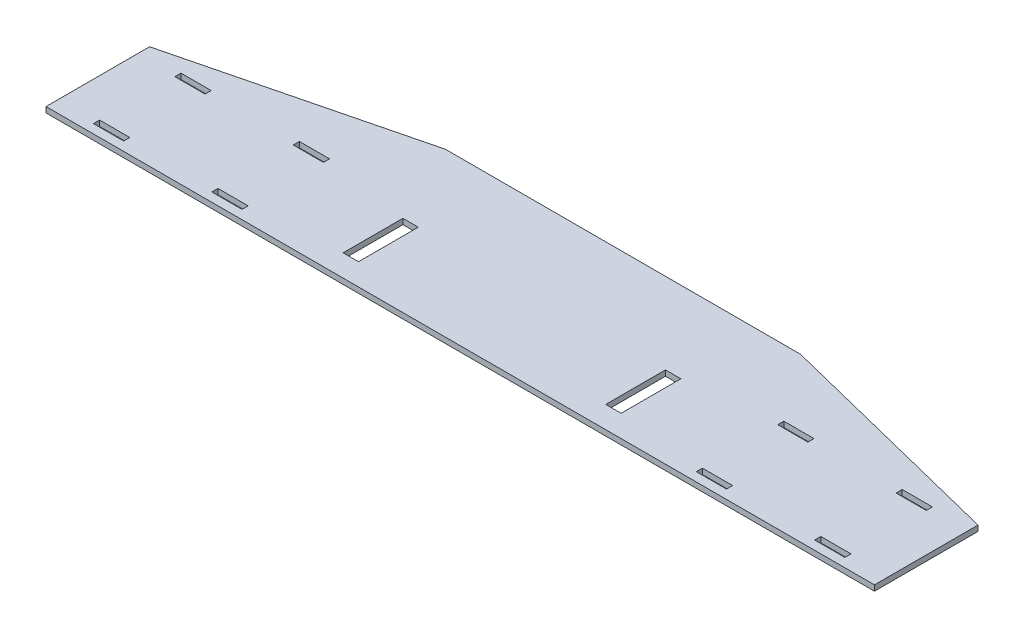
SolidWorks part; units mm, degrees
material "Plain Carbon Steel"
ref_plane "Front Plane" through (0, 0, 0) normal (0, 0, 1) x (1, 0, 0)
ref_plane "Top Plane" through (0, 0, 0) normal (0, 1, 0) x (1, 0, 0)
ref_plane "Right Plane" through (0, 0, 0) normal (1, 0, 0) x (0, 0, -1)
sketch "Sketch1" plane through (0, 0, 0) normal (0, 1, 0) x (1, 0, 0)
  line L1 (-355.6, 0) -> (355.6, 0)
  line L2 (-355.6, 0) -> (-355.6, 139.7)
  line L3 (-355.6, 139.7) -> (355.6, 139.7)
  line L4 (355.6, 0) -> (355.6, 139.7)
  dimension "D1" = 711.2
  dimension "D2" = 139.7
extrude "Boss-Extrude1" add sketch "Sketch1" along normal blind 4.7625
sketch "Sketch2" plane through (0, 4.7625, 0) normal (0, 1, 0) x (1, 0, 0)
  line L0 (-355.6, 88.9) -> (-152.4, 139.7)
  line L1 (-355.6, 139.7) -> (-355.6, 0) construction
  line L2 (355.6, 139.7) -> (-355.6, 139.7) construction
  line L3 (-152.4, 139.7) -> (-355.6, 139.7)
  line L4 (-355.6, 139.7) -> (-355.6, 88.9)
  line L5 (355.6, 139.7) -> (152.4, 139.7)
  line L6 (152.4, 139.7) -> (355.6, 88.9)
  line L7 (355.6, 0) -> (355.6, 139.7) construction
  line L8 (355.6, 88.9) -> (355.6, 139.7)
  dimension "D1" = 203.2
  dimension "D2" = 50.8
extrude "Cut-Extrude1" cut sketch "Sketch2" against normal through all
sketch "Sketch3" plane through (0, 0, 0) normal (0, -1, 0) x (-1, 0, 0)
  line L0 (-119.3165, 70.104) -> (-106.1085, 70.104)
  line L1 (119.0625, 19.05) -> (106.3625, 19.05)
  line L2 (119.0625, 19.05) -> (119.0625, 69.85)
  line L3 (119.0625, 69.85) -> (106.3625, 69.85)
  line L4 (106.3625, 19.05) -> (106.3625, 69.85)
  line L5 (-119.0625, 19.05) -> (-106.3625, 19.05)
  line L6 (-119.0625, 19.05) -> (-119.0625, 69.85)
  line L7 (-119.0625, 69.85) -> (-106.3625, 69.85)
  line L8 (-106.3625, 19.05) -> (-106.3625, 69.85)
  line L9 (-106.1085, 18.796) -> (-106.1085, 70.104)
  line L10 (-119.3165, 18.796) -> (-106.1085, 18.796)
  line L11 (-119.3165, 18.796) -> (-119.3165, 70.104)
  line L12 (119.3165, 18.796) -> (106.1085, 18.796)
  line L13 (106.1085, 18.796) -> (106.1085, 70.104)
  line L14 (119.3165, 70.104) -> (106.1085, 70.104)
  line L15 (119.3165, 18.796) -> (119.3165, 70.104)
  dimension "D1" = 0.254
extrude "Cut-Extrude2" cut sketch "Sketch3" against normal through all
sketch "Sketch4" plane through (0, 0, 0) normal (0, -1, 0) x (1, 0, 0)
  line L0 (119.0625, -82.55) -> (322.2625, -82.55) construction
  line L1 (322.2625, -82.55) -> (296.8625, -82.55)
  line L2 (322.2625, -82.55) -> (322.2625, -77.7875)
  line L3 (322.2625, -77.7875) -> (296.8625, -77.7875)
  line L4 (296.8625, -82.55) -> (296.8625, -77.7875)
  line L5 (220.6625, -82.55) -> (195.2625, -82.55)
  line L6 (220.6625, -82.55) -> (220.6625, -77.7875)
  line L7 (220.6625, -77.7875) -> (195.2625, -77.7875)
  line L8 (195.2625, -82.55) -> (195.2625, -77.7875)
  line L9 (119.0625, -7.9375) -> (322.2625, -7.9375) construction
  line L10 (195.2625, -12.7) -> (220.6625, -12.7)
  line L11 (195.2625, -12.7) -> (195.2625, -7.9375)
  line L12 (195.2625, -7.9375) -> (220.6625, -7.9375)
  line L13 (220.6625, -12.7) -> (220.6625, -7.9375)
  line L14 (-220.9165, -12.954) -> (-220.9165, -7.6835)
  line L15 (296.8625, -12.7) -> (322.2625, -12.7)
  line L16 (296.8625, -12.7) -> (296.8625, -7.9375)
  line L17 (296.8625, -7.9375) -> (322.2625, -7.9375)
  line L18 (322.2625, -12.7) -> (322.2625, -7.9375)
  line L19 (-220.6625, -82.55) -> (-195.2625, -82.55)
  line L20 (-220.6625, -82.55) -> (-220.6625, -77.7875)
  line L21 (-220.6625, -77.7875) -> (-195.2625, -77.7875)
  line L22 (-195.2625, -82.55) -> (-195.2625, -77.7875)
  line L23 (-322.2625, -82.55) -> (-296.8625, -82.55)
  line L24 (-322.2625, -82.55) -> (-322.2625, -77.7875)
  line L25 (-322.2625, -77.7875) -> (-296.8625, -77.7875)
  line L26 (-296.8625, -82.55) -> (-296.8625, -77.7875)
  line L27 (-322.2625, -12.7) -> (-296.8625, -12.7)
  line L28 (-322.2625, -12.7) -> (-322.2625, -7.9375)
  line L29 (-322.2625, -7.9375) -> (-296.8625, -7.9375)
  line L30 (-296.8625, -12.7) -> (-296.8625, -7.9375)
  line L31 (-220.6625, -12.7) -> (-195.2625, -12.7)
  line L32 (-220.6625, -12.7) -> (-220.6625, -7.9375)
  line L33 (-220.6625, -7.9375) -> (-195.2625, -7.9375)
  line L34 (-195.2625, -12.7) -> (-195.2625, -7.9375)
  line L35 (-220.9165, -7.6835) -> (-195.0085, -7.6835)
  line L36 (-195.0085, -12.954) -> (-195.0085, -7.6835)
  line L37 (-220.9165, -12.954) -> (-195.0085, -12.954)
  line L38 (-220.9165, -77.5335) -> (-195.0085, -77.5335)
  line L39 (-195.0085, -82.804) -> (-195.0085, -77.5335)
  line L40 (-220.9165, -82.804) -> (-195.0085, -82.804)
  line L41 (-220.9165, -82.804) -> (-220.9165, -77.5335)
  line L42 (-322.5165, -77.5335) -> (-296.6085, -77.5335)
  line L43 (-296.6085, -82.804) -> (-296.6085, -77.5335)
  line L44 (-322.5165, -82.804) -> (-296.6085, -82.804)
  line L45 (-322.5165, -82.804) -> (-322.5165, -77.5335)
  line L46 (-322.5165, -7.6835) -> (-296.6085, -7.6835)
  line L47 (-296.6085, -12.954) -> (-296.6085, -7.6835)
  line L48 (-322.5165, -12.954) -> (-296.6085, -12.954)
  line L49 (-322.5165, -12.954) -> (-322.5165, -7.6835)
  line L50 (220.9165, -77.5335) -> (195.0085, -77.5335)
  line L51 (195.0085, -82.804) -> (195.0085, -77.5335)
  line L52 (220.9165, -82.804) -> (195.0085, -82.804)
  line L53 (220.9165, -82.804) -> (220.9165, -77.5335)
  line L54 (322.5165, -77.5335) -> (296.6085, -77.5335)
  line L55 (296.6085, -82.804) -> (296.6085, -77.5335)
  line L56 (322.5165, -82.804) -> (296.6085, -82.804)
  line L57 (322.5165, -82.804) -> (322.5165, -77.5335)
  line L58 (296.6085, -7.6835) -> (322.5165, -7.6835)
  line L59 (322.5165, -12.954) -> (322.5165, -7.6835)
  line L60 (296.6085, -12.954) -> (322.5165, -12.954)
  line L61 (296.6085, -12.954) -> (296.6085, -7.6835)
  line L62 (195.0085, -7.6835) -> (220.9165, -7.6835)
  line L63 (220.9165, -12.954) -> (220.9165, -7.6835)
  line L64 (195.0085, -12.954) -> (220.9165, -12.954)
  line L65 (195.0085, -12.954) -> (195.0085, -7.6835)
  dimension "D1" = 0.254
extrude "Cut-Extrude3" cut sketch "Sketch4" against normal through all
